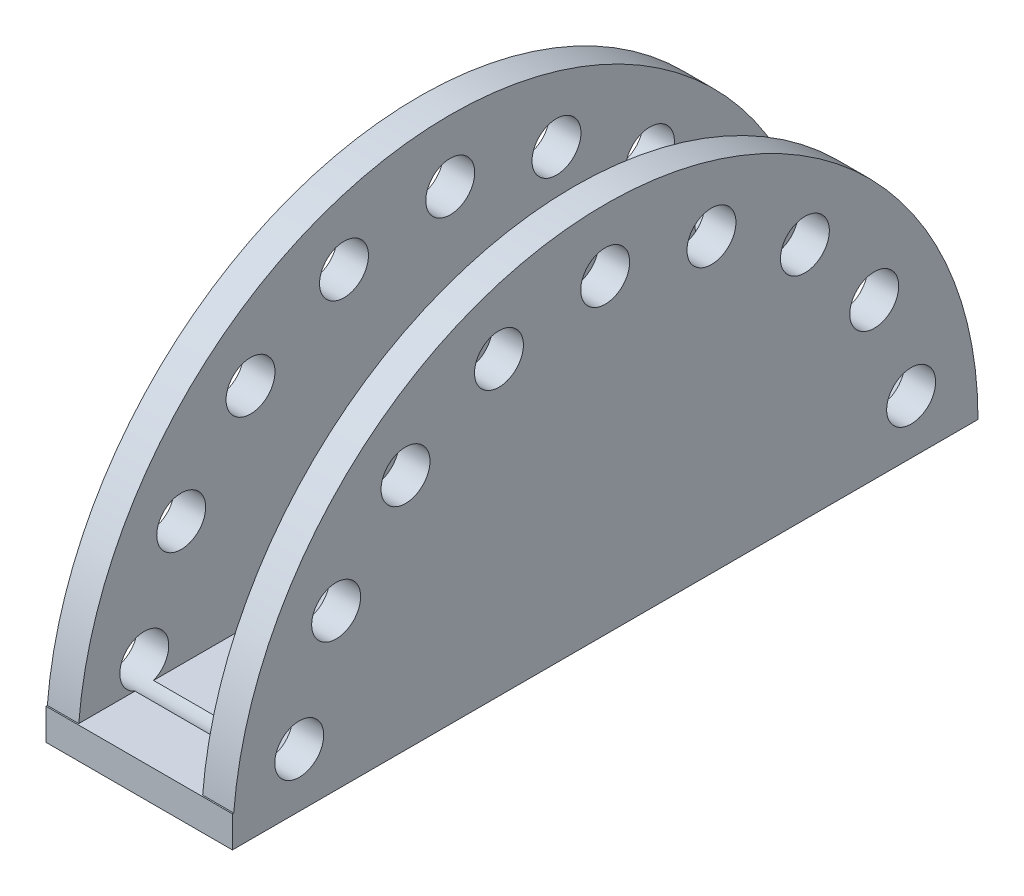
SolidWorks part; units mm, degrees
ref_plane "Front Plane" through (0, 0, 0) normal (0, 0, 1) x (1, 0, 0)
ref_plane "Top Plane" through (0, 0, 0) normal (0, 1, 0) x (1, 0, 0)
ref_plane "Right Plane" through (0, 0, 0) normal (1, 0, 0) x (0, 0, -1)
sketch "Sketch1" plane through (0, 0, 0) normal (1, 0, 0) x (0, 0, -1)
  line L0 (-76.2, 0) -> (76.2, 0)
  arc A0 (76.2, 0) -> (-76.2, 0) centre (0, 0) ccw
extrude "Boss-Extrude1" add sketch "Sketch1" along normal blind 38.1
sketch "Sketch2" plane through (0, 0, 0) normal (0, -1, 0) x (1, 0, 0)
  line L0 (38.1, 76.2) -> (38.1, -76.2) construction
  line L1 (6.4262, 80.2387) -> (31.75, 80.2387)
  line L2 (6.4262, 80.2387) -> (6.4262, -80.4518)
  line L3 (6.4262, -80.4518) -> (31.75, -80.4518)
  line L4 (31.75, 80.2387) -> (31.75, -80.4518)
  line L5 (0, 76.2) -> (0, -76.2) construction
  dimension "D1" = 6.35
  dimension "D2" = 6.4262
extrude "Cut-Extrude1" cut sketch "Sketch2" against normal through all
sketch "Sketch3" plane through (38.1, 0, 0) normal (1, 0, 0) x (0, 0, -1)
  line L0 (-76.2, 0) -> (76.2, 0) construction
  line L1 (-76.2, 0) -> (75.9309, 0)
  line L2 (-76.2, 0) -> (-76.2, 6.3988)
  line L3 (-76.2, 6.3988) -> (75.9309, 6.3988)
  line L4 (75.9309, 0) -> (75.9309, 6.3988)
  arc A0 (76.2, 0) -> (-76.2, 0) centre (0, 0) ccw construction
extrude "Boss-Extrude2" add sketch "Sketch3" against normal blind 38.1
sketch "Sketch4" plane through (38.1, 0, 0) normal (1, 0, 0) x (0, 0, -1)
  line L0 (0, 0) -> (0, 76.2) construction
  arc A0 (76.2, 0) -> (-75.9309, 6.3988) centre (0, 0) ccw construction
  circle A1 centre (0, 63.5) radius 5
  circle A2 centre (21.7183, 59.6705) radius 5
  circle A3 centre (40.817, 48.6438) radius 5
  circle A4 centre (54.9926, 31.75) radius 5
  circle A5 centre (62.5353, 11.0267) radius 5
  circle A15 centre (-62.5353, 11.0267) radius 5
  circle A16 centre (-54.9926, 31.75) radius 5
  circle A17 centre (-40.817, 48.6438) radius 5
  circle A18 centre (-21.7183, 59.6705) radius 5
  point P45 (0, 0)
  dimension "D1" = 10
  dimension "D2" = 12.7
extrude "Cut-Extrude2" cut sketch "Sketch4" against normal through all
